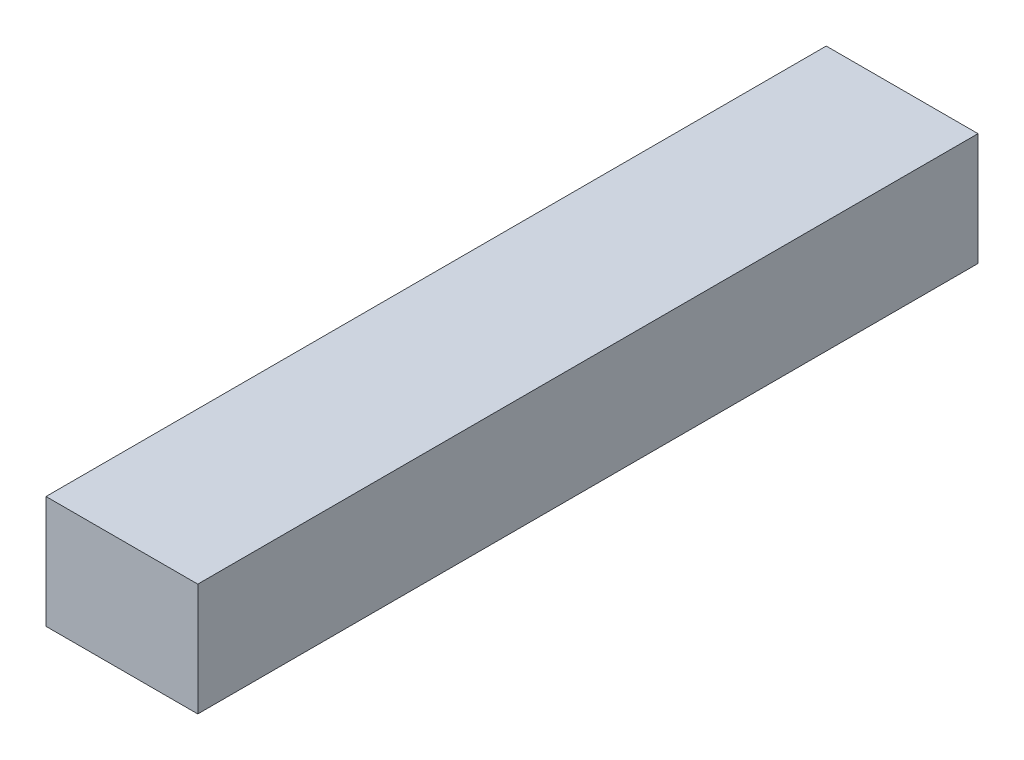
SolidWorks part; units mm, degrees
ref_plane "Plan de face" through (0, 0, 0) normal (0, 0, 1) x (1, 0, 0)
ref_plane "Plan de dessus" through (0, 0, 0) normal (0, 1, 0) x (1, 0, 0)
ref_plane "Plan de droite" through (0, 0, 0) normal (1, 0, 0) x (0, 0, -1)
sketch "Esquisse1" plane through (0, 0, 0) normal (0, 0, 1) x (1, 0, 0)
  line L1 (-3.9, -2.89) -> (3.9, -2.89)
  line L2 (-3.9, -2.89) -> (-3.9, 2.89)
  line L3 (-3.9, 2.89) -> (3.9, 2.89)
  line L4 (3.9, -2.89) -> (3.9, 2.89)
  line L5 (-3.9, -2.89) -> (3.9, 2.89) construction
  line L6 (-3.9, 2.89) -> (3.9, -2.89) construction
  point P0 (0, 0)
  dimension "D1" = 5.78
  dimension "D2" = 7.8
extrude "Boss.-Extru.1" add sketch "Esquisse1" along normal blind 40.1
